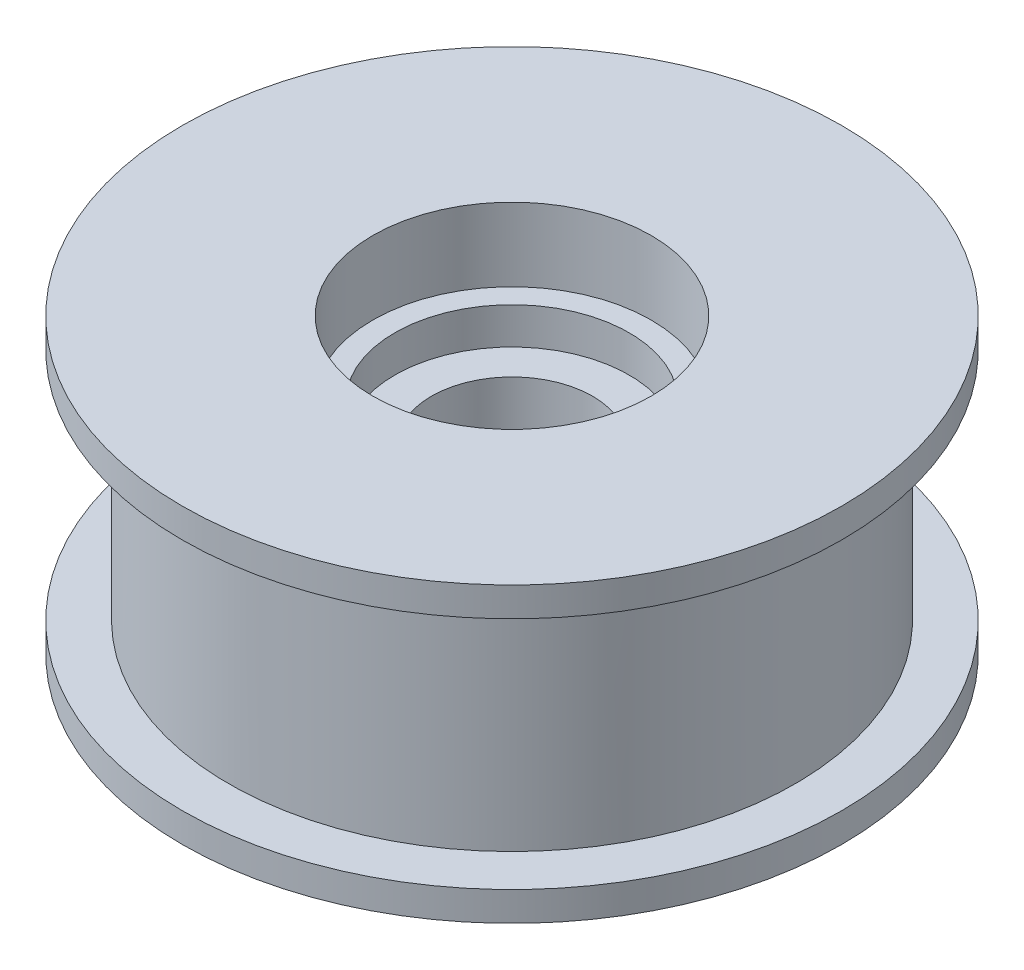
SolidWorks part; units mm, degrees
material "6061 合金"
ref_plane "前视基准面" through (0, 0, 0) normal (0, 0, 1) x (1, 0, 0)
ref_plane "上视基准面" through (0, 0, 0) normal (0, 1, 0) x (1, 0, 0)
ref_plane "右视基准面" through (0, 0, 0) normal (1, 0, 0) x (0, 0, -1)
sketch "草图1" plane through (0, 0, 0) normal (0, 1, 0) x (1, 0, 0)
  circle A0 centre (0, 0) radius 2.5
  circle A1 centre (0, 0) radius 19.325
  dimension "D1" = 5
  dimension "D2" = 38.65
extrude "凸台-拉伸1" add sketch "草图1" along normal blind 16
sketch "草图2" plane through (0, 16, 0) normal (0, 1, 0) x (1, 0, 0)
  circle A0 centre (0, 0) radius 22.5
  circle A1 centre (0, 0) radius 2.5
  dimension "D1" = 45
extrude "凸台-拉伸2" add sketch "草图2" along normal blind 2
sketch "草图3" plane through (0, 0, 0) normal (0, -1, 0) x (1, 0, 0)
  circle A0 centre (0, 0) radius 2.5
  circle A1 centre (0, 0) radius 22.5
  dimension "D1" = 45
extrude "凸台-拉伸3" add sketch "草图3" along normal blind 2
sketch "草图4" plane through (0, -2, 0) normal (0, -1, 0) x (1, 0, 0)
  circle A0 centre (0, 0) radius 5.5
  dimension "D1" = 11
extrude "切除-拉伸1" cut sketch "草图4" against normal up to surface (20 mm away) up to face at (0, 18, 22.5)
sketch "草图5" plane through (0, -2, 0) normal (0, -1, 0) x (1, 0, 0)
  circle A0 centre (0, 0) radius 8 construction
  point P3 (0, 8)
  point P4 (8, 0)
  point P5 (0, -8)
  point P6 (-8, 0)
  point P14 (0, 0)
  dimension "D1" = 16
hole_wizard "M3 螺纹孔1" positions "3D草图1" profile "草图6" tap size "M3" standard "GB"
sketch3d "3D草图1"
  point P0 (0, -2, 8)
  point P3 (8, -2, 0)
  point P6 (0, -2, -8)
  point P9 (-8, -2, 0)
sketch "草图6" plane through (0, -2, 8) normal (1, 0, 0) x (0, 0, -1)
  line L0 (0, 0) -> (0, 9.2511)
  line L1 (0, 9.2511) -> (1.25, 8.5)
  line L2 (1.25, 8.5) -> (1.25, 0)
  line L5 (1.25, 0) -> (0, 0)
  line L10 (0, 9.2511) -> (-1.25, 8.5) construction
  line L11 (0, -6.35) -> (0, 107.95) construction
  dimension "螺纹孔钻头直径" = 2.5
  dimension "螺纹孔钻头深度" = 8.5
  dimension "导头角度" = 118
cosmetic thread "孔螺蚊线1" parameters "D1"=6, "D2"=3
cosmetic thread "孔螺蚊线2" parameters "D1"=6, "D2"=3
cosmetic thread "孔螺蚊线3" parameters "D1"=6, "D2"=3
cosmetic thread "孔螺蚊线4" parameters "D1"=6, "D2"=3
sketch "草图7" plane through (0, 18, 0) normal (0, 1, 0) x (1, 0, 0)
  circle A0 centre (0, 0) radius 9.5
  dimension "D1" = 19
extrude "切除-拉伸3" cut sketch "草图7" against normal blind 5
sketch "草图8" plane through (0, 13, 0) normal (0, 1, 0) x (1, 0, 0)
  circle A0 centre (0, 0) radius 8
  dimension "D1" = 16
extrude "切除-拉伸4" cut sketch "草图8" against normal blind 2.5
